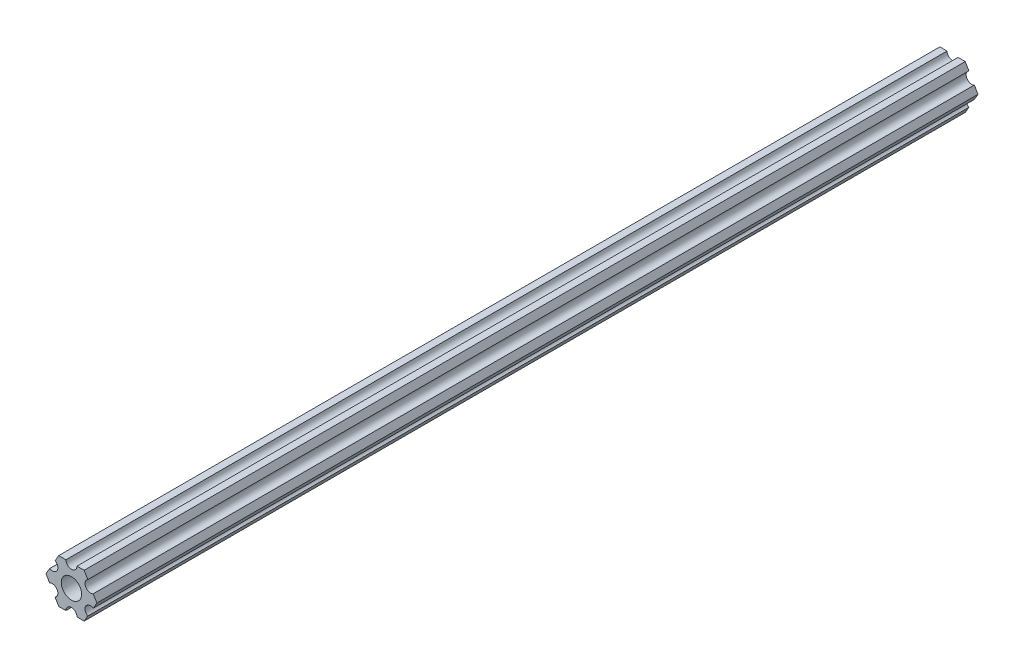
SolidWorks part; units mm, degrees
material "6061-T6 (SS)"
ref_plane "Front Plane" through (0, 0, 0) normal (0, 0, 1) x (1, 0, 0)
ref_plane "Top Plane" through (0, 0, 0) normal (0, 1, 0) x (1, 0, 0)
ref_plane "Right Plane" through (0, 0, 0) normal (1, 0, 0) x (0, 0, -1)
sketch "Sketch1" plane through (0, 0, 0) normal (0, 0, 1) x (1, 0, 0)
  line L0 (-4.7055, -4.5498) -> (-3.6662, -6.35)
  line L1 (-3.6662, -6.35) -> (-1.5875, -6.35)
  line L2 (1.5875, -6.35) -> (3.6662, -6.35)
  line L3 (3.6662, -6.35) -> (4.7055, -4.5498)
  line L4 (6.293, -1.8002) -> (7.3323, 0)
  line L5 (7.3323, 0) -> (6.293, 1.8002)
  line L6 (4.7055, 4.5498) -> (3.6662, 6.35)
  line L7 (3.6662, 6.35) -> (1.5875, 6.35)
  line L8 (-1.5875, 6.35) -> (-3.6662, 6.35)
  line L9 (-3.6662, 6.35) -> (-4.7055, 4.5498)
  line L10 (-6.293, 1.8002) -> (-7.3323, 0)
  line L11 (-7.3323, 0) -> (-6.293, -1.8002)
  circle A0 centre (0, 0) radius 2.9337
  arc A1 (-6.293, -1.8002) -> (-4.7055, -4.5498) centre (-5.4993, -3.175) cw
  arc A2 (-1.5875, -6.35) -> (1.5875, -6.35) centre (0, -6.35) cw
  arc A3 (4.7055, -4.5498) -> (6.293, -1.8002) centre (5.4993, -3.175) cw
  arc A4 (6.293, 1.8002) -> (4.7055, 4.5498) centre (5.4993, 3.175) cw
  arc A5 (1.5875, 6.35) -> (-1.5875, 6.35) centre (0, 6.35) cw
  arc A6 (-4.7055, 4.5498) -> (-6.293, 1.8002) centre (-5.4993, 3.175) cw
extrude "Boss-Extrude1" add sketch "Sketch1" against normal blind 254
